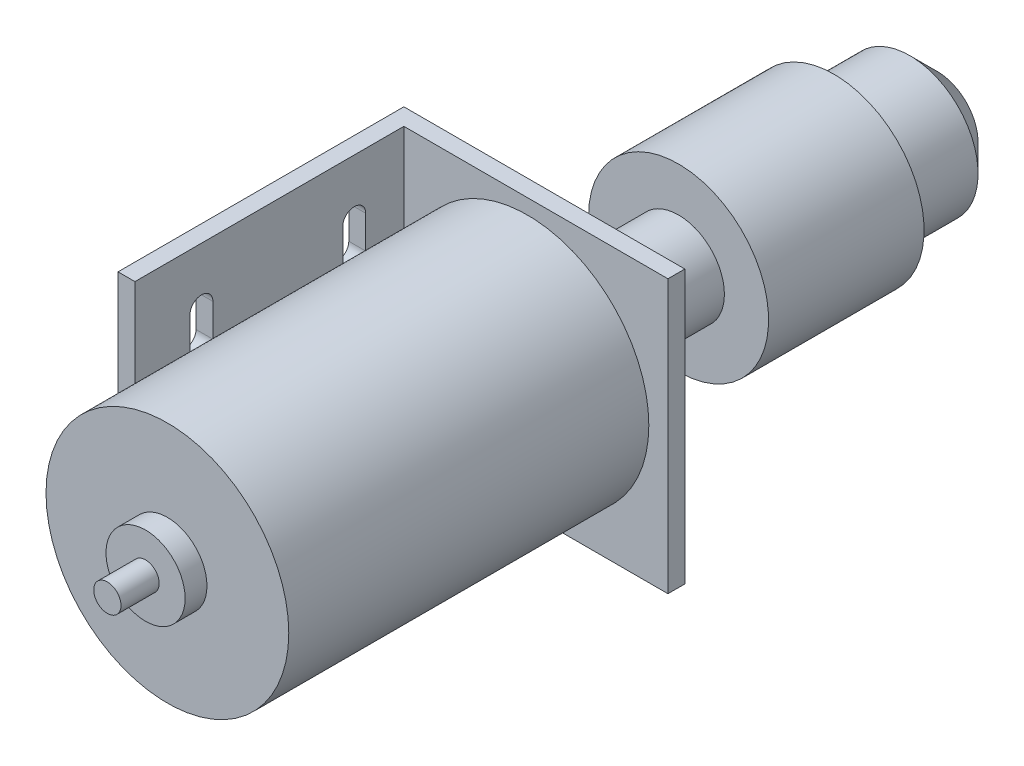
SolidWorks part; units mm, degrees
ref_plane "Front Plane" through (0, 0, 0) normal (0, 0, 1) x (1, 0, 0)
ref_plane "Top Plane" through (0, 0, 0) normal (0, 1, 0) x (1, 0, 0)
ref_plane "Right Plane" through (0, 0, 0) normal (1, 0, 0) x (0, 0, -1)
sketch "Sketch1" plane through (0, 0, 0) normal (0, 0, 1) x (1, 0, 0)
  circle A0 centre (0, 0) radius 22.25
  dimension "D1" = 44.5
extrude "Boss-Extrude1" add sketch "Sketch1" along normal blind 66
sketch "Sketch2" plane through (0, 0, 66) normal (0, 0, 1) x (1, 0, 0)
  circle A0 centre (0, 0) radius 7.25
  dimension "D1" = 14.5
extrude "Boss-Extrude2" add sketch "Sketch2" along normal blind 4
sketch "Sketch3" plane through (0, 0, 70) normal (0, 0, 1) x (1, 0, 0)
  circle A0 centre (0, 0) radius 2.5
  dimension "D1" = 5
extrude "Boss-Extrude3" add sketch "Sketch3" along normal blind 7
sketch "Sketch4" plane through (0, 0, 0) normal (0, 0, -1) x (-1, 0, 0)
  line L1 (-25.75, -25) -> (25.75, -25)
  line L2 (-25.75, -25) -> (-25.75, 25)
  line L3 (-25.75, 25) -> (25.75, 25)
  line L4 (25.75, -25) -> (25.75, 25)
  line L5 (-25.75, -25) -> (25.75, 25) construction
  line L6 (-25.75, 25) -> (25.75, -25) construction
  circle A0 centre (0, 0) radius 8.6
  point P0 (0, 0)
  dimension "D3" = 17.2
  dimension "D1" = 51.5
  dimension "D2" = 50
extrude "Boss-Extrude4" add sketch "Sketch4" along normal blind 3.1
sketch "Sketch5" plane through (0, 0, 0) normal (0, 0, -1) x (-1, 0, 0)
  circle A0 centre (0, 0) radius 8.4
  circle A1 centre (0, 0) radius 8.6 construction
  dimension "D1" = 0.2
extrude "Boss-Extrude5" add sketch "Sketch5" along normal blind 27.7
sketch "Sketch6" plane through (0, 0, -27.7) normal (0, 0, -1) x (-1, 0, 0)
  circle A0 centre (0, 0) radius 16.5
  dimension "D1" = 33
extrude "Boss-Extrude6" add sketch "Sketch6" along normal blind 28.5
sketch "Sketch7" plane through (0, 0, -56.2) normal (0, 0, -1) x (-1, 0, 0)
  circle A0 centre (0, 0) radius 12.5
  dimension "D1" = 25
extrude "Boss-Extrude7" add sketch "Sketch7" along normal blind 18.9
sketch "Sketch8" plane through (0, 0, -75.1) normal (0, 0, -1) x (-1, 0, 0)
  circle A0 centre (0, 0) radius 5.3
  dimension "D1" = 10.6
extrude "Cut-Extrude1" cut sketch "Sketch8" against normal blind 26.4
chamfer "Chamfer1" distance 5 angle 45 1 edges at (-12.5, 0, -75.1)
sketch "Sketch9" plane through (0, 0, 0) normal (0, 0, 1) x (1, 0, 0)
  line L5 (25.75, -25) -> (-25.75, -25) construction
  line L6 (-25.75, 25) -> (-22.65, 25)
  line L7 (-25.75, 25) -> (-25.75, -25)
  line L8 (-25.75, -25) -> (-22.65, -25)
  line L9 (-22.65, 25) -> (-22.65, -25)
  dimension "D1" = 3.1
extrude "Boss-Extrude8" add sketch "Sketch9" along normal blind 49.3
sketch "Sketch10" plane through (-25.75, 0, 0) normal (-1, 0, 0) x (0, 0, 1)
  line L0 (49.3, 0) -> (-3.1, 0) construction
  line L1 (49.3, 25) -> (49.3, -25) construction
  line L2 (-3.1, -25) -> (-3.1, 25) construction
  line L3 (23.1, 25) -> (23.1, -25) construction
  line L4 (-3.1, 25) -> (49.3, 25) construction
  line L5 (-3.1, -25) -> (49.3, -25) construction
  line L6 (37.1, 14.7) -> (37.1, 8.7) construction
  line L7 (39.2, 14.7) -> (39.2, 8.7)
  line L8 (35, 14.7) -> (35, 8.7)
  line L9 (37.1, -14.7) -> (37.1, -8.7) construction
  line L10 (39.2, -14.7) -> (39.2, -8.7)
  line L11 (35, -14.7) -> (35, -8.7)
  line L12 (9.1, -14.7) -> (9.1, -8.7) construction
  line L13 (7, -14.7) -> (7, -8.7)
  line L14 (11.2, -14.7) -> (11.2, -8.7)
  line L15 (9.1, 14.7) -> (9.1, 8.7) construction
  line L16 (7, 14.7) -> (7, 8.7)
  line L17 (11.2, 14.7) -> (11.2, 8.7)
  arc A0 (39.2, 14.7) -> (35, 14.7) centre (37.1, 14.7) ccw
  arc A1 (35, 8.7) -> (39.2, 8.7) centre (37.1, 8.7) ccw
  arc A2 (39.2, -14.7) -> (35, -14.7) centre (37.1, -14.7) cw
  arc A3 (35, -8.7) -> (39.2, -8.7) centre (37.1, -8.7) cw
  arc A4 (7, -14.7) -> (11.2, -14.7) centre (9.1, -14.7) ccw
  arc A5 (11.2, -8.7) -> (7, -8.7) centre (9.1, -8.7) ccw
  arc A6 (7, 14.7) -> (11.2, 14.7) centre (9.1, 14.7) cw
  arc A7 (11.2, 8.7) -> (7, 8.7) centre (9.1, 8.7) cw
  circle A8 centre (37.1, 11.7) radius 2.1 construction
  point P14 (37.1, 11.7)
  point P19 (37.1, 16.8)
  point P20 (37.1, 6.6)
  point P23 (37.1, -11.7)
  point P30 (9.1, -11.7)
  point P37 (9.1, 11.7)
  dimension "D2" = 2.1
  dimension "D3" = 6.6
  dimension "D1" = 10.2
  dimension "D4" = 11.9
extrude "Cut-Extrude2" cut sketch "Sketch10" against normal up to next
